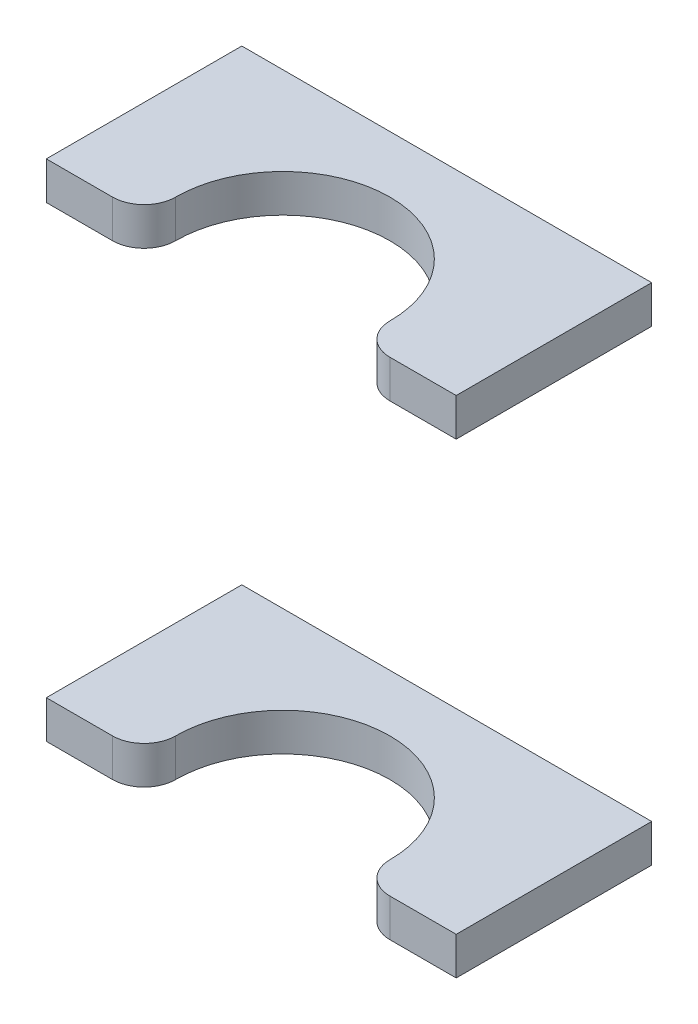
SolidWorks part; units mm, degrees
material "Plain Carbon Steel"
ref_plane "Front Plane" through (0, 0, 0) normal (0, 0, 1) x (1, 0, 0)
ref_plane "Top Plane" through (0, 0, 0) normal (0, 1, 0) x (1, 0, 0)
ref_plane "Right Plane" through (0, 0, 0) normal (1, 0, 0) x (0, 0, -1)
sketch "Sketch1" plane through (0, 0, 0) normal (0, 0, 1) x (1, 0, 0)
  line L0 (-347.5, 0) -> (-347.5, 120) construction
  line L1 (660, 0) -> (-660, 0) construction
  line L2 (-660, 120) -> (660, 120) construction
  line L3 (-347.5, 60) -> (-213.0727, 60) construction
  line L4 (-315, 20) -> (-380, 20)
  line L5 (-315, 20) -> (-315, 26)
  line L6 (-315, 26) -> (-380, 26)
  line L7 (-380, 20) -> (-380, 26)
  line L8 (-315, 20) -> (-380, 26) construction
  line L9 (-315, 26) -> (-380, 20) construction
  line L10 (-315, 94) -> (-380, 100) construction
  line L11 (-315, 100) -> (-380, 94) construction
  line L12 (-380, 100) -> (-380, 94)
  line L13 (-315, 94) -> (-380, 94)
  line L14 (-315, 100) -> (-315, 94)
  line L15 (-315, 100) -> (-380, 100)
  line L16 (-420, 120) -> (-420, -340) construction
  point P6 (-347.5, 23)
  point P17 (-347.5, 97)
  dimension "D1" = 6
  dimension "D2" = 65
  dimension "D3" = 20
  dimension "D4" = 40
extrude "Boss-Extrude1" add sketch "Sketch1" along normal up to surface (46 mm away)
sketch "Sketch4" plane through (0, 20, 0) normal (0, -1, 0) x (-1, 0, 0)
  line L0 (420, -26) -> (315, -26) construction
  line L1 (420, -41) -> (420, -11) construction
  line L2 (315, -46) -> (315, 0) construction
  line L3 (347.5, -46) -> (347.5, -26) construction
  line L4 (380, -46) -> (315, -46) construction
  line L5 (315, -31) -> (315, -46)
  line L6 (380, -31) -> (380, -46)
  line L7 (380, -46) -> (315, -46)
  line L9 (369.5, -31) -> (380, -31)
  line L12 (325.5, -31) -> (315, -31)
  arc A0 (364.5, -26) -> (330.5, -26) centre (347.5, -26) ccw
  arc A1 (364.5, -26) -> (369.5, -31) centre (369.5, -26) ccw
  arc A2 (330.5, -26) -> (325.5, -31) centre (325.5, -26) cw
  dimension "D1" = 34
  dimension "D2" = 5
extrude "Cut-Extrude4" cut sketch "Sketch4" against normal through all
